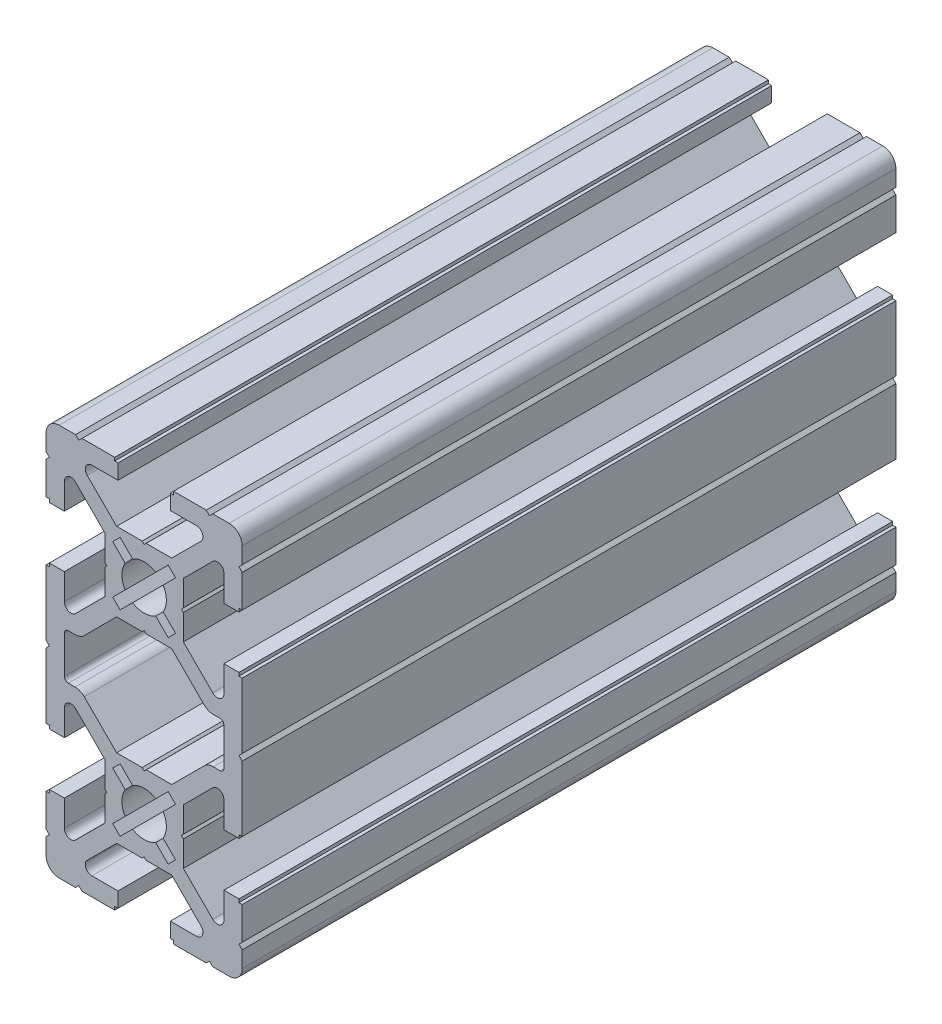
SolidWorks part; units mm, degrees
ref_plane "Ön Düzlem" through (0, 0, 0) normal (0, 0, 1) x (1, 0, 0)
ref_plane "Üst Düzlem" through (0, 0, 0) normal (0, 1, 0) x (1, 0, 0)
ref_plane "Sağ Düzlem" through (0, 0, 0) normal (1, 0, 0) x (0, 0, -1)
ref_plane "Düzlem1" through (0, 0, 100) normal (0, 0, 1) x (1, 0, 0)
sketch "Çizim1" plane through (0, 0, 100) normal (0, 0, 1) x (1, 0, 0)
  line L0 (-2.9023, 16.771) -> (-4.8083, 18.677)
  line L1 (-4.8083, 18.677) -> (-3.677, 19.8083)
  line L2 (-3.677, 19.8083) -> (-1.771, 17.9023)
  line L3 (1.771, 17.9023) -> (3.677, 19.8083)
  line L4 (3.677, 19.8083) -> (4.8083, 18.677)
  line L5 (4.8083, 18.677) -> (2.9023, 16.771)
  line L6 (2.9023, 13.229) -> (4.8083, 11.323)
  line L7 (4.8083, 11.323) -> (3.677, 10.1917)
  line L8 (3.677, 10.1917) -> (1.771, 12.0977)
  line L9 (-1.771, 12.0977) -> (-3.677, 10.1917)
  line L10 (-3.677, 10.1917) -> (-4.8083, 11.323)
  line L11 (-4.8083, 11.323) -> (-2.9023, 13.229)
  line L12 (-2.9023, -13.229) -> (-4.8083, -11.323)
  line L13 (-4.8083, -11.323) -> (-3.677, -10.1917)
  line L14 (-3.677, -10.1917) -> (-1.771, -12.0977)
  line L15 (1.771, -12.0977) -> (3.677, -10.1917)
  line L16 (3.677, -10.1917) -> (4.8083, -11.323)
  line L17 (4.8083, -11.323) -> (2.9023, -13.229)
  line L18 (2.9023, -16.771) -> (4.8083, -18.677)
  line L19 (4.8083, -18.677) -> (3.677, -19.8083)
  line L20 (3.677, -19.8083) -> (1.771, -17.9023)
  line L21 (-1.771, -17.9023) -> (-3.677, -19.8083)
  line L22 (-3.677, -19.8083) -> (-4.8083, -18.677)
  line L23 (-4.8083, -18.677) -> (-2.9023, -16.771)
  line L24 (-9.1584, 4.0558) -> (-4.2142, 9)
  line L25 (-4.2142, 9) -> (-0.3125, 9)
  line L26 (-0.3125, 9) -> (0, 9.3)
  line L27 (0, 9.3) -> (0.3125, 9)
  line L28 (0.3125, 9) -> (4.2142, 9)
  line L29 (4.2142, 9) -> (9.1584, 4.0558)
  line L30 (10.5726, 3.47) -> (11.6, 3.47)
  line L31 (12.2, 2.87) -> (12.2, -2.87)
  line L32 (11.6, -3.47) -> (10.5726, -3.47)
  line L33 (9.1584, -4.0558) -> (4.2142, -9)
  line L34 (4.2142, -9) -> (0.3125, -9)
  line L35 (0.3125, -9) -> (0, -9.3)
  line L36 (0, -9.3) -> (-0.3125, -9)
  line L37 (-0.3125, -9) -> (-4.2142, -9)
  line L38 (-4.2142, -9) -> (-9.1584, -4.0558)
  line L39 (-10.5726, -3.47) -> (-11.6, -3.47)
  line L40 (-12.2, -2.87) -> (-12.2, 2.87)
  line L41 (-11.6, 3.47) -> (-10.5726, 3.47)
  line L42 (-4.2142, 21) -> (-8.7071, 25.4929)
  line L43 (-8, 27.2) -> (-4, 27.2)
  line L44 (-4, 27.2) -> (-4, 29.5)
  line L45 (-4, 29.5) -> (-4.5, 29.5)
  line L46 (-4.5, 29.5) -> (-4.5, 30)
  line L47 (-4.5, 30) -> (-9.5, 30)
  line L48 (-9.5, 30) -> (-10, 29.5)
  line L49 (-10, 29.5) -> (-10.5, 30)
  line L50 (-10.5, 30) -> (-13, 30)
  line L51 (-15, 28) -> (-15, 25.5)
  line L52 (-15, 25.5) -> (-14.5, 25)
  line L53 (-14.5, 25) -> (-15, 24.5)
  line L54 (-15, 24.5) -> (-15, 19.5)
  line L55 (-15, 19.5) -> (-14.5, 19.5)
  line L56 (-14.5, 19.5) -> (-14.5, 19)
  line L57 (-14.5, 19) -> (-12.2, 19)
  line L58 (-12.2, 19) -> (-12.2, 23)
  line L59 (-10.4929, 23.7071) -> (-6, 19.2142)
  line L60 (-6, 19.2142) -> (-6, 15.3125)
  line L61 (-6, 15.3125) -> (-5.7, 15)
  line L62 (-5.7, 15) -> (-6, 14.6875)
  line L63 (-6, 14.6875) -> (-6, 10.7858)
  line L64 (-6, 10.7858) -> (-10.4929, 6.2929)
  line L65 (-12.2, 7) -> (-12.2, 11)
  line L66 (-12.2, 11) -> (-14.5, 11)
  line L67 (-14.5, 11) -> (-14.5, 10.5)
  line L68 (-14.5, 10.5) -> (-15, 10.5)
  line L69 (-15, 10.5) -> (-15, 0.5)
  line L70 (-15, 0.5) -> (-14.5, 0)
  line L71 (-14.5, 0) -> (-15, -0.5)
  line L72 (-15, -0.5) -> (-15, -10.5)
  line L73 (-15, -10.5) -> (-14.5, -10.5)
  line L74 (-14.5, -10.5) -> (-14.5, -11)
  line L75 (-14.5, -11) -> (-12.2, -11)
  line L76 (-12.2, -11) -> (-12.2, -7)
  line L77 (-10.4929, -6.2929) -> (-6, -10.7858)
  line L78 (-6, -10.7858) -> (-6, -14.6875)
  line L79 (-6, -14.6875) -> (-5.7, -15)
  line L80 (-5.7, -15) -> (-6, -15.3125)
  line L81 (-6, -15.3125) -> (-6, -19.2142)
  line L82 (-6, -19.2142) -> (-10.4929, -23.7071)
  line L83 (-12.2, -23) -> (-12.2, -19)
  line L84 (-12.2, -19) -> (-14.5, -19)
  line L85 (-14.5, -19) -> (-14.5, -19.5)
  line L86 (-14.5, -19.5) -> (-15, -19.5)
  line L87 (-15, -19.5) -> (-15, -24.5)
  line L88 (-15, -24.5) -> (-14.5, -25)
  line L89 (-14.5, -25) -> (-15, -25.5)
  line L90 (-15, -25.5) -> (-15, -28)
  line L91 (-13, -30) -> (-10.5, -30)
  line L92 (-10.5, -30) -> (-10, -29.5)
  line L93 (-10, -29.5) -> (-9.5, -30)
  line L94 (-9.5, -30) -> (-4.5, -30)
  line L95 (-4.5, -30) -> (-4.5, -29.5)
  line L96 (-4.5, -29.5) -> (-4, -29.5)
  line L97 (-4, -29.5) -> (-4, -27.2)
  line L98 (-4, -27.2) -> (-8, -27.2)
  line L99 (-8.7071, -25.4929) -> (-4.2142, -21)
  line L100 (-4.2142, -21) -> (-0.3125, -21)
  line L101 (-0.3125, -21) -> (0, -20.7)
  line L102 (0, -20.7) -> (0.3125, -21)
  line L103 (0.3125, -21) -> (4.2142, -21)
  line L104 (4.2142, -21) -> (8.7071, -25.4929)
  line L105 (8, -27.2) -> (4, -27.2)
  line L106 (4, -27.2) -> (4, -29.5)
  line L107 (4, -29.5) -> (4.5, -29.5)
  line L108 (4.5, -29.5) -> (4.5, -30)
  line L109 (4.5, -30) -> (9.5, -30)
  line L110 (9.5, -30) -> (10, -29.5)
  line L111 (10, -29.5) -> (10.5, -30)
  line L112 (10.5, -30) -> (13, -30)
  line L113 (15, -28) -> (15, -25.5)
  line L114 (15, -25.5) -> (14.5, -25)
  line L115 (14.5, -25) -> (15, -24.5)
  line L116 (15, -24.5) -> (15, -19.5)
  line L117 (15, -19.5) -> (14.5, -19.5)
  line L118 (14.5, -19.5) -> (14.5, -19)
  line L119 (14.5, -19) -> (12.2, -19)
  line L120 (12.2, -19) -> (12.2, -23)
  line L121 (10.4929, -23.7071) -> (6, -19.2142)
  line L122 (6, -19.2142) -> (6, -15.3125)
  line L123 (6, -15.3125) -> (5.7, -15)
  line L124 (5.7, -15) -> (6, -14.6875)
  line L125 (6, -14.6875) -> (6, -10.7858)
  line L126 (6, -10.7858) -> (10.4929, -6.2929)
  line L127 (12.2, -7) -> (12.2, -11)
  line L128 (12.2, -11) -> (14.5, -11)
  line L129 (14.5, -11) -> (14.5, -10.5)
  line L130 (14.5, -10.5) -> (15, -10.5)
  line L131 (15, -10.5) -> (15, -0.5)
  line L132 (15, -0.5) -> (14.5, 0)
  line L133 (14.5, 0) -> (15, 0.5)
  line L134 (15, 0.5) -> (15, 10.5)
  line L135 (15, 10.5) -> (14.5, 10.5)
  line L136 (14.5, 10.5) -> (14.5, 11)
  line L137 (14.5, 11) -> (12.2, 11)
  line L138 (12.2, 11) -> (12.2, 7)
  line L139 (10.4929, 6.2929) -> (6, 10.7858)
  line L140 (6, 10.7858) -> (6, 14.6875)
  line L141 (6, 14.6875) -> (5.7, 15)
  line L142 (5.7, 15) -> (6, 15.3125)
  line L143 (6, 15.3125) -> (6, 19.2142)
  line L144 (6, 19.2142) -> (10.4929, 23.7071)
  line L145 (12.2, 23) -> (12.2, 19)
  line L146 (12.2, 19) -> (14.5, 19)
  line L147 (14.5, 19) -> (14.5, 19.5)
  line L148 (14.5, 19.5) -> (15, 19.5)
  line L149 (15, 19.5) -> (15, 24.5)
  line L150 (15, 24.5) -> (14.5, 25)
  line L151 (14.5, 25) -> (15, 25.5)
  line L152 (15, 25.5) -> (15, 28)
  line L153 (13, 30) -> (10.5, 30)
  line L154 (10.5, 30) -> (10, 29.5)
  line L155 (10, 29.5) -> (9.5, 30)
  line L156 (9.5, 30) -> (4.5, 30)
  line L157 (4.5, 30) -> (4.5, 29.5)
  line L158 (4.5, 29.5) -> (4, 29.5)
  line L159 (4, 29.5) -> (4, 27.2)
  line L160 (4, 27.2) -> (8, 27.2)
  line L161 (8.7071, 25.4929) -> (4.2142, 21)
  line L162 (4.2142, 21) -> (0.3125, 21)
  line L163 (0.3125, 21) -> (0, 20.7)
  line L164 (0, 20.7) -> (-0.3125, 21)
  line L165 (-0.3125, 21) -> (-4.2142, 21)
  arc A0 (-1.771, 17.9023) -> (1.771, 17.9023) centre (0, 15) cw
  arc A1 (2.9023, 16.771) -> (2.9023, 13.229) centre (0, 15) cw
  arc A2 (1.771, 12.0977) -> (-1.771, 12.0977) centre (0, 15) cw
  arc A3 (-2.9023, 13.229) -> (-2.9023, 16.771) centre (0, 15) cw
  arc A4 (-1.771, -12.0977) -> (1.771, -12.0977) centre (0, -15) cw
  arc A5 (2.9023, -13.229) -> (2.9023, -16.771) centre (0, -15) cw
  arc A6 (1.771, -17.9023) -> (-1.771, -17.9023) centre (0, -15) cw
  arc A7 (-2.9023, -16.771) -> (-2.9023, -13.229) centre (0, -15) cw
  arc A8 (9.1584, 4.0558) -> (10.5726, 3.47) centre (10.5726, 5.47) ccw
  arc A9 (11.6, 3.47) -> (12.2, 2.87) centre (11.6, 2.87) cw
  arc A10 (12.2, -2.87) -> (11.6, -3.47) centre (11.6, -2.87) cw
  arc A11 (10.5726, -3.47) -> (9.1584, -4.0558) centre (10.5726, -5.47) ccw
  arc A12 (-9.1584, -4.0558) -> (-10.5726, -3.47) centre (-10.5726, -5.47) ccw
  arc A13 (-11.6, -3.47) -> (-12.2, -2.87) centre (-11.6, -2.87) cw
  arc A14 (-12.2, 2.87) -> (-11.6, 3.47) centre (-11.6, 2.87) cw
  arc A15 (-10.5726, 3.47) -> (-9.1584, 4.0558) centre (-10.5726, 5.47) ccw
  arc A16 (-8.7071, 25.4929) -> (-8, 27.2) centre (-8, 26.2) cw
  arc A17 (-13, 30) -> (-15, 28) centre (-13, 28) ccw
  arc A18 (-12.2, 23) -> (-10.4929, 23.7071) centre (-11.2, 23) cw
  arc A19 (-10.4929, 6.2929) -> (-12.2, 7) centre (-11.2, 7) cw
  arc A20 (-12.2, -7) -> (-10.4929, -6.2929) centre (-11.2, -7) cw
  arc A21 (-10.4929, -23.7071) -> (-12.2, -23) centre (-11.2, -23) cw
  arc A22 (-15, -28) -> (-13, -30) centre (-13, -28) ccw
  arc A23 (-8, -27.2) -> (-8.7071, -25.4929) centre (-8, -26.2) cw
  arc A24 (8.7071, -25.4929) -> (8, -27.2) centre (8, -26.2) cw
  arc A25 (13, -30) -> (15, -28) centre (13, -28) ccw
  arc A26 (12.2, -23) -> (10.4929, -23.7071) centre (11.2, -23) cw
  arc A27 (10.4929, -6.2929) -> (12.2, -7) centre (11.2, -7) cw
  arc A28 (12.2, 7) -> (10.4929, 6.2929) centre (11.2, 7) cw
  arc A29 (10.4929, 23.7071) -> (12.2, 23) centre (11.2, 23) cw
  arc A30 (15, 28) -> (13, 30) centre (13, 28) ccw
  arc A31 (8, 27.2) -> (8.7071, 25.4929) centre (8, 26.2) cw
extrude "Yükseklik-Ekstrüzyon1" add sketch "Çizim1" against normal blind 100
